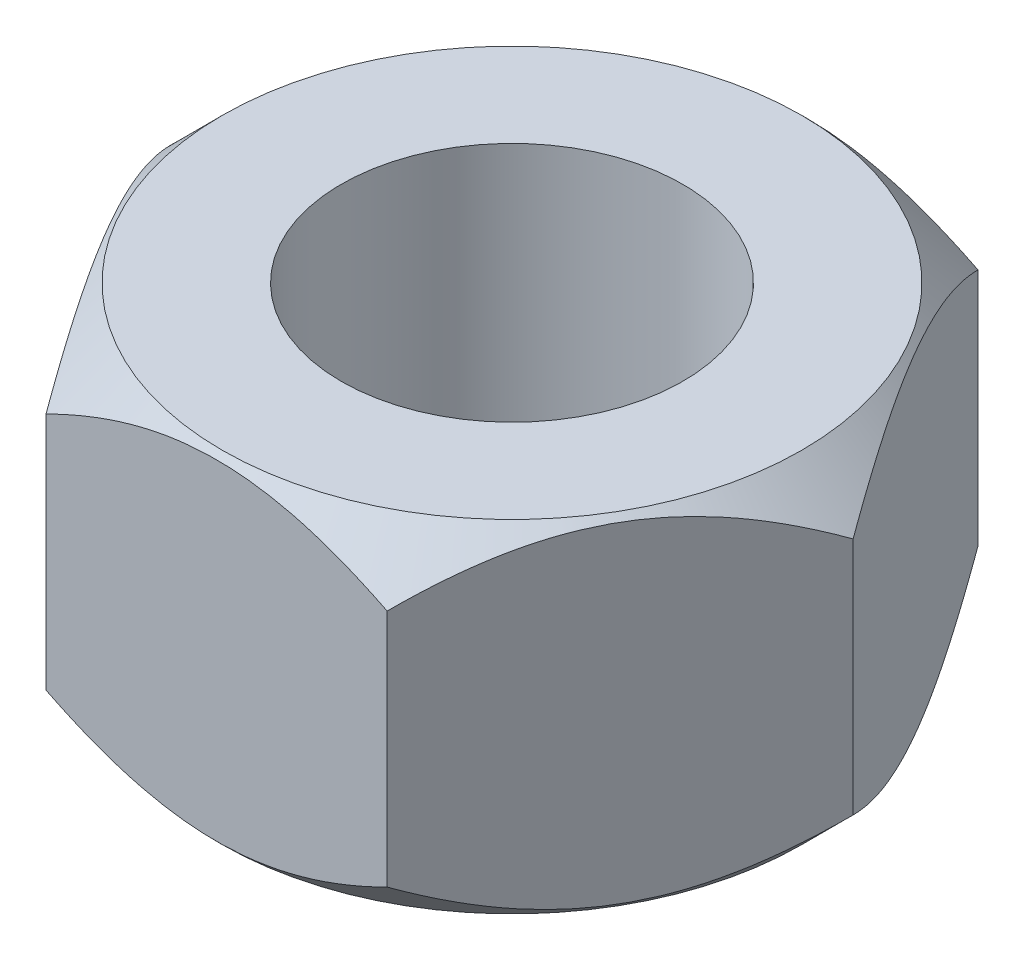
SolidWorks part; units mm, degrees
ref_plane "Front Plane" through (0, 0, 0) normal (0, 0, 1) x (1, 0, 0)
ref_plane "Top Plane" through (0, 0, 0) normal (0, 1, 0) x (1, 0, 0)
ref_plane "Right Plane" through (0, 0, 0) normal (1, 0, 0) x (0, 0, -1)
sketch "Sketch5" plane through (0, 0, 0) normal (0, 1, 0) x (1, 0, 0)
  line L1 (19.9763, 0) -> (9.9882, 17.3)
  line L2 (9.9882, 17.3) -> (-9.9882, 17.3)
  line L3 (-9.9882, 17.3) -> (-19.9763, 0)
  line L4 (-19.9763, 0) -> (-9.9882, -17.3)
  line L5 (-9.9882, -17.3) -> (9.9882, -17.3)
  line L6 (9.9882, -17.3) -> (19.9763, 0)
  circle A0 centre (0, 0) radius 17.3 construction
  circle A1 centre (0, 0) radius 10
  dimension "D2" = 20
  dimension "D1" = 34.6
extrude "Boss-Extrude1" add sketch "Sketch5" along normal blind 20
sketch "Sketch6" plane through (0, 0, 0) normal (0, 0, 1) x (1, 0, 0)
  line L0 (9.9882, 0) -> (19.9763, 0) construction
  line L1 (9.9882, 20) -> (19.9763, 20) construction
  line L2 (19.9763, 0) -> (16.9763, 0)
  line L3 (19.9763, 20) -> (16.9763, 20)
  line L4 (19.9763, 17) -> (19.9763, 20)
  line L5 (19.9763, 20) -> (19.9763, 0) construction
  line L6 (19.9763, 3) -> (19.9763, 0)
  line L7 (16.9763, 20) -> (19.9763, 17)
  line L8 (16.9763, 0) -> (19.9763, 3)
  line L9 (0, 0) -> (0, 4.4204) construction
revolve "Cut-Revolve1" cut sketch "Sketch6" angle 360 about L9
